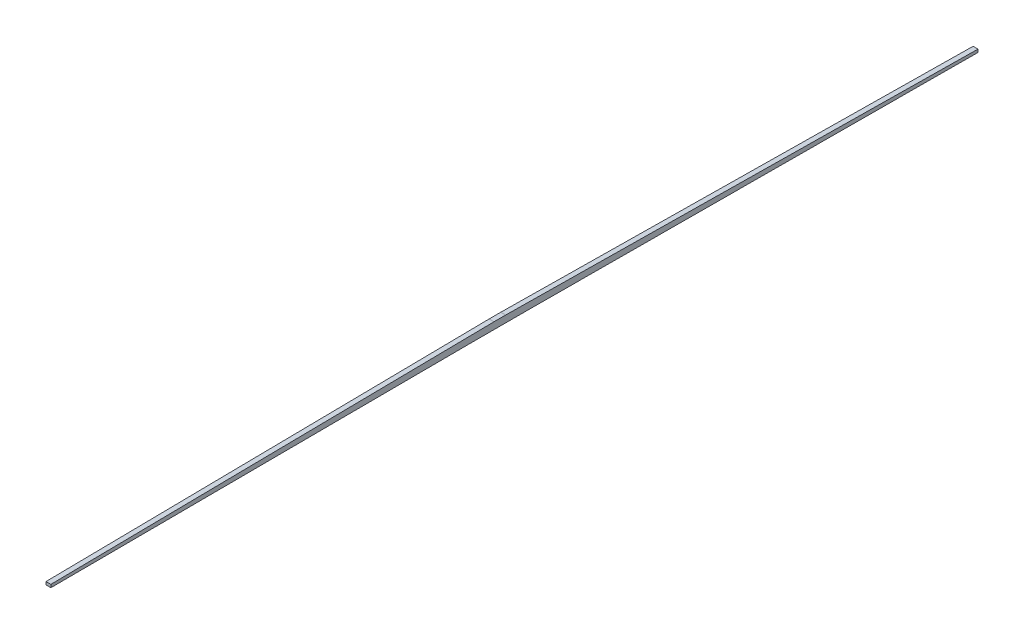
SolidWorks part; units mm, degrees
material "Beech"
ref_plane "Front" through (0, 0, 0) normal (0, 0, 1) x (1, 0, 0)
ref_plane "Top" through (0, 0, 0) normal (0, 1, 0) x (1, 0, 0)
ref_plane "Right" through (0, 0, 0) normal (1, 0, 0) x (0, 0, -1)
sketch "Sketch1" plane through (0, 0, 0) normal (1, 0, 0) x (0, 0, -1)
  line L0 (6, 0) -> (490, -6)
  line L1 (-6, 0) -> (6, 0)
  line L2 (490, -6) -> (490, -9)
  line L3 (-30, -7) -> (30, -7)
  line L4 (490, -9) -> (30, -7)
  line L5 (-30, -7) -> (-460, -9)
  line L6 (-460, -9) -> (-460, -6)
  line L7 (-460, -6) -> (-6, 0)
  line L8 (0, 0) -> (0, -7) construction
  dimension "D1" = 12
  dimension "D2" = 6
  dimension "D3" = 3
  dimension "D4" = 7
  dimension "D5" = 60
  dimension "D6" = 490
  dimension "D7" = 460
extrude "Extrude1" add sketch "Sketch1" along normal blind 5
